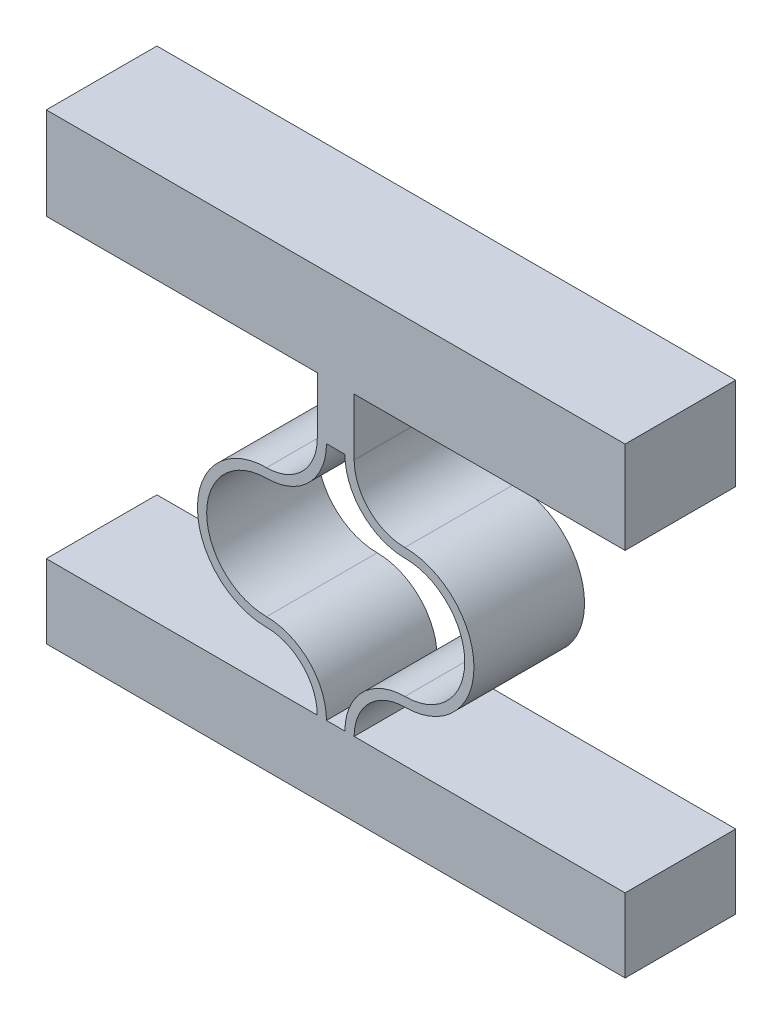
SolidWorks part; units mm, degrees
ref_plane "Front Plane" through (0, 0, 0) normal (0, 0, 1) x (1, 0, 0)
ref_plane "Top Plane" through (0, 0, 0) normal (0, 1, 0) x (1, 0, 0)
ref_plane "Right Plane" through (0, 0, 0) normal (1, 0, 0) x (0, 0, -1)
sketch "Sketch1" plane through (0, 0, 0) normal (0, 0, 1) x (1, 0, 0)
  line L4 (0, 10.5) -> (0, 0)
  line L5 (10.2, 0) -> (10.2, 13) construction
  line L6 (10.2, 13) -> (10.2, 15.9852) construction
  line L17 (9.7, 0) -> (0, 0)
  line L18 (10.7, 0) -> (20.4, 0)
  line L19 (20.4, 0) -> (20.4, 10.5)
  line L20 (10.7, 13.2452) -> (10.7, 14.4852)
  line L21 (9.7, 13.2452) -> (9.7, 14.4852)
  line L22 (10.7, 14.7452) -> (10.7, 15.9852)
  line L23 (10.7, 15.9852) -> (9.7, 15.9852)
  line L24 (9.7, 15.9852) -> (9.7, 14.7452)
  line L31 (-5, 12.26) -> (-5, -4)
  line L32 (-5, -4) -> (25.4, -4)
  line L33 (25.4, -4) -> (25.4, 12.26)
  line L34 (0, 10.76) -> (0, 12)
  line L36 (-5, 12.26) -> (0, 12.26)
  line L37 (25.4, 12.26) -> (20.4, 12.26)
  line L38 (20.4, 10.76) -> (20.4, 12)
  arc A0 (10.2, 13) -> (6.95, 9.75) centre (6.95, 13) cw
  arc A1 (6.95, 9.75) -> (6.95, 3.25) centre (6.95, 6.5) ccw
  arc A2 (6.95, 3.25) -> (10.2, 0) centre (6.95, 0) cw
  arc A3 (9.7, 12.9852) -> (6.95, 10.25) centre (6.95, 13) cw
  arc A4 (6.95, 10.25) -> (6.95, 2.75) centre (6.95, 6.5) ccw
  arc A5 (6.95, 2.75) -> (9.7, 0) centre (6.95, 0) cw
  arc A6 (9.7, 13) -> (6.95, 10.25) centre (6.95, 13) cw construction
  arc A7 (13.45, 3.25) -> (10.2, 0) centre (13.45, 0) ccw
  arc A8 (13.45, 2.75) -> (10.7, 0) centre (13.45, 0) ccw
  arc A9 (13.45, 9.75) -> (13.45, 3.25) centre (13.45, 6.5) cw
  arc A10 (13.45, 10.25) -> (13.45, 2.75) centre (13.45, 6.5) cw
  arc A11 (10.7, 12.9852) -> (13.45, 10.25) centre (13.45, 13) ccw
  arc A12 (10.2, 13) -> (13.45, 9.75) centre (13.45, 13) ccw
  spline S0 degree 4 poles (-2.0399, 10.9987) (-1.9769, 10.9844) (-1.8506, 10.9568) (-1.6594, 10.9185) (-1.4063, 10.8738) (-1.1473, 10.836) (-0.8994, 10.8056) (-0.6275, 10.7825) (-0.4084, 10.7671) (-0.0945, 10.7598) (0.0489, 10.7593) (0.3554, 10.7653) (0.5833, 10.7785) (0.8327, 10.7992) (1.1232, 10.8326) (1.4148, 10.8743) (1.7521, 10.9345) (2.2064, 11.0333) (2.726, 11.1697) (3.2397, 11.3281) (3.7479, 11.5024) (4.1845, 11.6613) (4.5513, 11.7992) (4.9172, 11.9395) (5.2828, 12.0805) (5.7402, 12.2559) (6.427, 12.5125) (7.2136, 12.7819) (8.1107, 13.0284) (9.0261, 13.1932) (9.8075, 13.2661) (10.5925, 13.2661) (11.3739, 13.1932) (12.2893, 13.0284) (13.1864, 12.7819) (13.973, 12.5125) (14.6598, 12.2559) (15.2087, 12.0455) (15.6656, 11.8688) (16.1235, 11.6948) (16.6521, 11.5024) (17.1603, 11.3281) (17.6739, 11.1697) (18.1937, 11.0333) (18.5999, 10.9449) (18.8889, 10.8915) (19.1309, 10.8534) (19.3251, 10.827) (19.5196, 10.8048) (19.7158, 10.7868) (19.909, 10.7733) (20.1017, 10.7642) (20.3513, 10.7593) (20.4943, 10.7598) (20.8085, 10.7671) (21.0274, 10.7825) (21.2994, 10.8056) (21.5473, 10.836) (21.8063, 10.8738) (22.0594, 10.9185) (22.2506, 10.9568) (22.3769, 10.9844) (22.4399, 10.9987) knots 0 0 0 0 0 0.010251 0.020502 0.030753 0.041005 0.05113 0.061255 0.071381 0.081506 0.089265 0.097024 0.112543 0.120302 0.128061 0.143579 0.159098 0.174616 0.201648 0.22868 0.244198 0.259716 0.275235 0.290753 0.306271 0.32179 0.352826 0.40689 0.437927 0.468963 0.5 0.531037 0.562073 0.59311 0.647174 0.67821 0.693729 0.709247 0.740284 0.755802 0.77132 0.798352 0.825384 0.840902 0.856421 0.86418 0.871939 0.879698 0.887457 0.895217 0.902976 0.910735 0.918494 0.928619 0.938745 0.94887 0.958995 0.969247 0.979498 0.989749 1 1 1 1 1 construction
  spline S1 degree 4 poles (0, 10.76) (0.041, 10.76) (0.1243, 10.7608) (0.3554, 10.7653) (0.5833, 10.7785) (0.8327, 10.7992) (1.1232, 10.8326) (1.4148, 10.8743) (1.7521, 10.9345) (2.2064, 11.0333) (2.726, 11.1697) (3.2397, 11.3281) (3.7479, 11.5024) (4.1845, 11.6613) (4.5513, 11.7992) (4.9172, 11.9395) (5.2828, 12.0805) (5.7402, 12.2559) (6.427, 12.5125) (7.2136, 12.7819) (8.1107, 13.0284) (9.0261, 13.1932) (9.8075, 13.2661) (10.5925, 13.2661) (11.3739, 13.1932) (12.2893, 13.0284) (13.1864, 12.7819) (13.973, 12.5125) (14.6598, 12.2559) (15.2087, 12.0455) (15.6656, 11.8688) (16.1235, 11.6948) (16.6521, 11.5024) (17.1603, 11.3281) (17.6739, 11.1697) (18.1937, 11.0333) (18.5999, 10.9449) (18.8889, 10.8915) (19.1309, 10.8534) (19.3251, 10.827) (19.5196, 10.8048) (19.7158, 10.7868) (19.909, 10.7733) (20.1017, 10.7642) (20.2757, 10.7608) (20.359, 10.76) (20.4, 10.76) knots 0.081506 0.081506 0.081506 0.081506 0.081506 0.089265 0.097024 0.112543 0.120302 0.128061 0.143579 0.159098 0.174616 0.201648 0.22868 0.244198 0.259716 0.275235 0.290753 0.306271 0.32179 0.352826 0.40689 0.437927 0.468963 0.5 0.531037 0.562073 0.59311 0.647174 0.67821 0.693729 0.709247 0.740284 0.755802 0.77132 0.798352 0.825384 0.840902 0.856421 0.86418 0.871939 0.879698 0.887457 0.895217 0.902976 0.910735 0.918494 0.918494 0.918494 0.918494 0.918494
  spline S2 degree 4 poles (-2.0399, 12.2387) (-1.9769, 12.2244) (-1.8506, 12.1968) (-1.6594, 12.1585) (-1.4063, 12.1138) (-1.1473, 12.076) (-0.8994, 12.0456) (-0.6275, 12.0225) (-0.4084, 12.0071) (-0.0945, 11.9998) (0.0489, 11.9993) (0.3554, 12.0053) (0.5833, 12.0185) (0.8327, 12.0392) (1.1232, 12.0726) (1.4148, 12.1143) (1.7521, 12.1745) (2.2064, 12.2733) (2.726, 12.4097) (3.2397, 12.5681) (3.7479, 12.7424) (4.1845, 12.9013) (4.5513, 13.0392) (4.9172, 13.1795) (5.2828, 13.3205) (5.7402, 13.4959) (6.427, 13.7525) (7.2136, 14.0219) (8.1107, 14.2684) (9.0261, 14.4332) (9.8075, 14.5061) (10.5925, 14.5061) (11.3739, 14.4332) (12.2893, 14.2684) (13.1864, 14.0219) (13.973, 13.7525) (14.6598, 13.4959) (15.2087, 13.2855) (15.6656, 13.1088) (16.1235, 12.9348) (16.6521, 12.7424) (17.1603, 12.5681) (17.6739, 12.4097) (18.1937, 12.2733) (18.5999, 12.1849) (18.8889, 12.1315) (19.1309, 12.0934) (19.3251, 12.067) (19.5196, 12.0448) (19.7158, 12.0268) (19.909, 12.0133) (20.1017, 12.0042) (20.3513, 11.9993) (20.4943, 11.9998) (20.8085, 12.0071) (21.0274, 12.0225) (21.2994, 12.0456) (21.5473, 12.076) (21.8063, 12.1138) (22.0594, 12.1585) (22.2506, 12.1968) (22.3769, 12.2244) (22.4399, 12.2387) knots 0 0 0 0 0 0.010251 0.020502 0.030753 0.041005 0.05113 0.061255 0.071381 0.081506 0.089265 0.097024 0.112543 0.120302 0.128061 0.143579 0.159098 0.174616 0.201648 0.22868 0.244198 0.259716 0.275235 0.290753 0.306271 0.32179 0.352826 0.40689 0.437927 0.468963 0.5 0.531037 0.562073 0.59311 0.647174 0.67821 0.693729 0.709247 0.740284 0.755802 0.77132 0.798352 0.825384 0.840902 0.856421 0.86418 0.871939 0.879698 0.887457 0.895217 0.902976 0.910735 0.918494 0.928619 0.938745 0.94887 0.958995 0.969247 0.979498 0.989749 1 1 1 1 1 construction
  spline S3 degree 4 poles (0, 12) (0.041, 12) (0.1243, 12.0008) (0.3554, 12.0053) (0.5833, 12.0185) (0.8327, 12.0392) (1.1232, 12.0726) (1.4148, 12.1143) (1.7521, 12.1745) (2.2064, 12.2733) (2.726, 12.4097) (3.2397, 12.5681) (3.7479, 12.7424) (4.1845, 12.9013) (4.5513, 13.0392) (4.9172, 13.1795) (5.2828, 13.3205) (5.7402, 13.4959) (6.427, 13.7525) (7.2136, 14.0219) (8.1107, 14.2684) (9.0261, 14.4332) (9.8075, 14.5061) (10.5925, 14.5061) (11.3739, 14.4332) (12.2893, 14.2684) (13.1864, 14.0219) (13.973, 13.7525) (14.6598, 13.4959) (15.2087, 13.2855) (15.6656, 13.1088) (16.1235, 12.9348) (16.6521, 12.7424) (17.1603, 12.5681) (17.6739, 12.4097) (18.1937, 12.2733) (18.5999, 12.1849) (18.8889, 12.1315) (19.1309, 12.0934) (19.3251, 12.067) (19.5196, 12.0448) (19.7158, 12.0268) (19.909, 12.0133) (20.1017, 12.0042) (20.2757, 12.0008) (20.359, 12) (20.4, 12) knots 0.081506 0.081506 0.081506 0.081506 0.081506 0.089265 0.097024 0.112543 0.120302 0.128061 0.143579 0.159098 0.174616 0.201648 0.22868 0.244198 0.259716 0.275235 0.290753 0.306271 0.32179 0.352826 0.40689 0.437927 0.468963 0.5 0.531037 0.562073 0.59311 0.647174 0.67821 0.693729 0.709247 0.740284 0.755802 0.77132 0.798352 0.825384 0.840902 0.856421 0.86418 0.871939 0.879698 0.887457 0.895217 0.902976 0.910735 0.918494 0.918494 0.918494 0.918494 0.918494
  spline S4 degree 4 poles (-2.0399, 12.4987) (-1.9769, 12.4844) (-1.8506, 12.4568) (-1.6594, 12.4185) (-1.4063, 12.3738) (-1.1473, 12.336) (-0.8994, 12.3056) (-0.6275, 12.2825) (-0.4084, 12.2671) (-0.0945, 12.2598) (0.0489, 12.2593) (0.3554, 12.2653) (0.5833, 12.2785) (0.8327, 12.2992) (1.1232, 12.3326) (1.4148, 12.3743) (1.7521, 12.4345) (2.2064, 12.5333) (2.726, 12.6697) (3.2397, 12.8281) (3.7479, 13.0024) (4.1845, 13.1613) (4.5513, 13.2992) (4.9172, 13.4395) (5.2828, 13.5805) (5.7402, 13.7559) (6.427, 14.0125) (7.2136, 14.2819) (8.1107, 14.5284) (9.0261, 14.6932) (9.8075, 14.7661) (10.5925, 14.7661) (11.3739, 14.6932) (12.2893, 14.5284) (13.1864, 14.2819) (13.973, 14.0125) (14.6598, 13.7559) (15.2087, 13.5455) (15.6656, 13.3688) (16.1235, 13.1948) (16.6521, 13.0024) (17.1603, 12.8281) (17.6739, 12.6697) (18.1937, 12.5333) (18.5999, 12.4449) (18.8889, 12.3915) (19.1309, 12.3534) (19.3251, 12.327) (19.5196, 12.3048) (19.7158, 12.2868) (19.909, 12.2733) (20.1017, 12.2642) (20.3513, 12.2593) (20.4943, 12.2598) (20.8085, 12.2671) (21.0274, 12.2825) (21.2994, 12.3056) (21.5473, 12.336) (21.8063, 12.3738) (22.0594, 12.4185) (22.2506, 12.4568) (22.3769, 12.4844) (22.4399, 12.4987) knots 0 0 0 0 0 0.010251 0.020502 0.030753 0.041005 0.05113 0.061255 0.071381 0.081506 0.089265 0.097024 0.112543 0.120302 0.128061 0.143579 0.159098 0.174616 0.201648 0.22868 0.244198 0.259716 0.275235 0.290753 0.306271 0.32179 0.352826 0.40689 0.437927 0.468963 0.5 0.531037 0.562073 0.59311 0.647174 0.67821 0.693729 0.709247 0.740284 0.755802 0.77132 0.798352 0.825384 0.840902 0.856421 0.86418 0.871939 0.879698 0.887457 0.895217 0.902976 0.910735 0.918494 0.928619 0.938745 0.94887 0.958995 0.969247 0.979498 0.989749 1 1 1 1 1 construction
  spline S5 degree 4 poles (0, 12.26) (0.041, 12.26) (0.1243, 12.2608) (0.3554, 12.2653) (0.5833, 12.2785) (0.8327, 12.2992) (1.1232, 12.3326) (1.4148, 12.3743) (1.7521, 12.4345) (2.2064, 12.5333) (2.726, 12.6697) (3.2397, 12.8281) (3.7479, 13.0024) (4.1845, 13.1613) (4.5513, 13.2992) (4.9172, 13.4395) (5.2828, 13.5805) (5.7402, 13.7559) (6.427, 14.0125) (7.2136, 14.2819) (8.1107, 14.5284) (9.0261, 14.6932) (9.8075, 14.7661) (10.5925, 14.7661) (11.3739, 14.6932) (12.2893, 14.5284) (13.1864, 14.2819) (13.973, 14.0125) (14.6598, 13.7559) (15.2087, 13.5455) (15.6656, 13.3688) (16.1235, 13.1948) (16.6521, 13.0024) (17.1603, 12.8281) (17.6739, 12.6697) (18.1937, 12.5333) (18.5999, 12.4449) (18.8889, 12.3915) (19.1309, 12.3534) (19.3251, 12.327) (19.5196, 12.3048) (19.7158, 12.2868) (19.909, 12.2733) (20.1017, 12.2642) (20.2757, 12.2608) (20.359, 12.26) (20.4, 12.26) knots 0.081506 0.081506 0.081506 0.081506 0.081506 0.089265 0.097024 0.112543 0.120302 0.128061 0.143579 0.159098 0.174616 0.201648 0.22868 0.244198 0.259716 0.275235 0.290753 0.306271 0.32179 0.352826 0.40689 0.437927 0.468963 0.5 0.531037 0.562073 0.59311 0.647174 0.67821 0.693729 0.709247 0.740284 0.755802 0.77132 0.798352 0.825384 0.840902 0.856421 0.86418 0.871939 0.879698 0.887457 0.895217 0.902976 0.910735 0.918494 0.918494 0.918494 0.918494 0.918494
  spline S8 degree 4 poles (-2.0399, 10.7387) (-1.9769, 10.7244) (-1.8506, 10.6968) (-1.6594, 10.6585) (-1.4063, 10.6138) (-1.1473, 10.576) (-0.8994, 10.5456) (-0.6275, 10.5225) (-0.4084, 10.5071) (-0.0945, 10.4998) (0.0489, 10.4993) (0.3554, 10.5053) (0.5833, 10.5185) (0.8327, 10.5392) (1.1232, 10.5726) (1.4148, 10.6143) (1.7521, 10.6745) (2.2064, 10.7733) (2.726, 10.9097) (3.2397, 11.0681) (3.7479, 11.2424) (4.1845, 11.4013) (4.5513, 11.5392) (4.9172, 11.6795) (5.2828, 11.8205) (5.7402, 11.9959) (6.427, 12.2525) (7.2136, 12.5219) (8.1107, 12.7684) (9.0261, 12.9332) (9.8075, 13.0061) (10.5925, 13.0061) (11.3739, 12.9332) (12.2893, 12.7684) (13.1864, 12.5219) (13.973, 12.2525) (14.6598, 11.9959) (15.2087, 11.7855) (15.6656, 11.6088) (16.1235, 11.4348) (16.6521, 11.2424) (17.1603, 11.0681) (17.6739, 10.9097) (18.1937, 10.7733) (18.5999, 10.6849) (18.8889, 10.6315) (19.1309, 10.5934) (19.3251, 10.567) (19.5196, 10.5448) (19.7158, 10.5268) (19.909, 10.5133) (20.1017, 10.5042) (20.3513, 10.4993) (20.4943, 10.4998) (20.8085, 10.5071) (21.0274, 10.5225) (21.2994, 10.5456) (21.5473, 10.576) (21.8063, 10.6138) (22.0594, 10.6585) (22.2506, 10.6968) (22.3769, 10.7244) (22.4399, 10.7387) knots 0 0 0 0 0 0.010251 0.020502 0.030753 0.041005 0.05113 0.061255 0.071381 0.081506 0.089265 0.097024 0.112543 0.120302 0.128061 0.143579 0.159098 0.174616 0.201648 0.22868 0.244198 0.259716 0.275235 0.290753 0.306271 0.32179 0.352826 0.40689 0.437927 0.468963 0.5 0.531037 0.562073 0.59311 0.647174 0.67821 0.693729 0.709247 0.740284 0.755802 0.77132 0.798352 0.825384 0.840902 0.856421 0.86418 0.871939 0.879698 0.887457 0.895217 0.902976 0.910735 0.918494 0.928619 0.938745 0.94887 0.958995 0.969247 0.979498 0.989749 1 1 1 1 1 construction
  spline S9 degree 4 poles (0, 10.5) (0.041, 10.5) (0.1243, 10.5008) (0.3554, 10.5053) (0.5833, 10.5185) (0.8327, 10.5392) (1.1232, 10.5726) (1.4148, 10.6143) (1.7521, 10.6745) (2.2064, 10.7733) (2.726, 10.9097) (3.2397, 11.0681) (3.7479, 11.2424) (4.1845, 11.4013) (4.5513, 11.5392) (4.9172, 11.6795) (5.2828, 11.8205) (5.7402, 11.9959) (6.427, 12.2525) (7.2136, 12.5219) (8.1107, 12.7684) (9.0261, 12.9332) (9.8075, 13.0061) (10.5925, 13.0061) (11.3739, 12.9332) (12.2893, 12.7684) (13.1864, 12.5219) (13.973, 12.2525) (14.6598, 11.9959) (15.2087, 11.7855) (15.6656, 11.6088) (16.1235, 11.4348) (16.6521, 11.2424) (17.1603, 11.0681) (17.6739, 10.9097) (18.1937, 10.7733) (18.5999, 10.6849) (18.8889, 10.6315) (19.1309, 10.5934) (19.3251, 10.567) (19.5196, 10.5448) (19.7158, 10.5268) (19.909, 10.5133) (20.1017, 10.5042) (20.2757, 10.5008) (20.359, 10.5) (20.4, 10.5) knots 0.081506 0.081506 0.081506 0.081506 0.081506 0.089265 0.097024 0.112543 0.120302 0.128061 0.143579 0.159098 0.174616 0.201648 0.22868 0.244198 0.259716 0.275235 0.290753 0.306271 0.32179 0.352826 0.40689 0.437927 0.468963 0.5 0.531037 0.562073 0.59311 0.647174 0.67821 0.693729 0.709247 0.740284 0.755802 0.77132 0.798352 0.825384 0.840902 0.856421 0.86418 0.871939 0.879698 0.887457 0.895217 0.902976 0.910735 0.918494 0.918494 0.918494 0.918494 0.918494
  dimension "D4" = 0.26
  dimension "D6" = 4
  dimension "D1" = 13
  dimension "D2" = 0.5
  dimension "D3" = 0.26
  dimension "D7" = 5
  dimension "D5" = 1.5
extrude "Boss-Extrude1" add sketch "Sketch1" along normal blind 6
sketch "Sketch4" plane through (0, 15.9852, 0) normal (0, 1, 0) x (1, 0, 0)
  line L24 (10.7, 0) -> (9.7, 0)
  line L25 (9.7, 0) -> (9.7, -6)
  line L26 (10.7, 0) -> (9.7, 0)
  line L27 (10.7, -6) -> (10.7, 0)
  line L29 (9.7, 0) -> (9.7, -6)
  line L31 (10.7, -6) -> (10.7, 0)
  line L32 (9.7, -6) -> (10.7, -6)
  line L33 (9.7, -6) -> (10.7, -6)
  dimension "D1" = 0
extrude "Boss-Extrude2" add sketch "Sketch4" along normal blind 0.1
mirror "Mirror3" [suppressed]
ref_plane "Plane1" through (10.2, 0, 0) normal (-1, 0, 0) x (0, 0, 1)
split "Split2" trim tools "Plane1" bodies to split 179 102 resulting bodies 225
sketch "Sketch7" plane through (10.2, 0, 0) normal (-1, 0, 0) x (0, 0, 1)
  line L4 (0, 13) -> (6, 13)
  line L12 (0, 13) -> (6, 13)
  line L13 (0, 13) -> (6, 13)
  line L14 (6, 13) -> (6, 16.0852)
  line L15 (6, 13) -> (6, 16.0852)
  line L20 (6, 0) -> (0, 0)
  line L22 (6, 0) -> (0, 0)
  line L23 (0, -4) -> (6, -4)
  line L27 (0, -4) -> (6, -4)
  line L31 (6, 16.0852) -> (0, 16.0852)
  line L33 (0, 16.0852) -> (0, 13)
  line L34 (0, 16.0852) -> (0, 13)
  line L36 (6, -4) -> (6, 0)
  line L38 (0, 13) -> (6, 13)
  line L39 (0, 13) -> (6, 13)
  line L40 (6, 13) -> (6, 16.0852)
  line L41 (6, 13) -> (6, 16.0852)
  line L51 (6, 16.0852) -> (0, 16.0852)
  line L52 (6, 16.0852) -> (0, 16.0852)
  line L53 (0, 16.0852) -> (0, 13)
  line L54 (0, 16.0852) -> (0, 13)
  line L55 (0, 13) -> (6, 13)
  line L59 (6, -4) -> (6, 0)
  line L60 (0, 0) -> (0, -4)
  line L61 (0, 0) -> (0, -4)
  line L62 (6, 13) -> (6, 16.0852)
  line L64 (6, 13) -> (6, 16.0852)
  line L66 (6, 16.0852) -> (0, 16.0852)
  line L67 (6, 16.0852) -> (0, 16.0852)
  line L68 (0, 16.0852) -> (0, 13)
  line L69 (0, 16.0852) -> (0, 13)
  line L70 (6, 16.0852) -> (0, 16.0852)
  dimension "D1" = 0
  dimension "D2" = 0
  dimension "D3" = 0
  dimension "D4" = 0
extrude "Boss-Extrude3" add sketch "Sketch7" along normal blind 0.5
mirror "Mirror2" about plane through (9.7, 0, 0) normal (-1, 0, 0) of bodies 226
sketch "Sketch8" plane through (0, 0, 6) normal (0, 0, 1) x (1, 0, 0)
  line L0 (25.4, 12.26) -> (20.4, 12.26) construction
  line L1 (-6, 21.0852) -> (25.4, 21.0852)
  line L2 (-6, 21.0852) -> (-6, 16.0852)
  line L3 (-6, 16.0852) -> (25.4, 16.0852)
  line L4 (25.4, 21.0852) -> (25.4, 16.0852)
  line L5 (25.4, -4) -> (25.4, 12.26) construction
  line L6 (-6, -4) -> (-6, 12.26) construction
  line L7 (8.7, 16.0852) -> (10.7, 16.0852) construction
extrude "Boss-Extrude4" add sketch "Sketch8" against normal up to surface (6 mm away) up to face at (9.7, 10.5186, 0)
sketch "Sketch9" plane through (0, 0, 6) normal (0, 0, 1) x (1, 0, 0)
  line L0 (-1, 10.5) -> (-1, 12.26)
  line L1 (20.4, 10.5) -> (20.4, 12.26)
  line L2 (10.7, 14.7452) -> (10.7, 12.9852)
  line L3 (8.7, 12.9852) -> (8.7, 14.7452)
  spline S0 degree 4 poles (-508.9824, 1946.5317) (8.084, -72.7533) (31.0872, 1.6312) (18.0938, 16.5066) (7.1107, 14.5284) (6.2136, 14.2819) (5.427, 14.0125) (4.7402, 13.7559) (4.1913, 13.5455) (3.7344, 13.3688) (3.2765, 13.1948) (2.7479, 13.0024) (2.2397, 12.8281) (1.7261, 12.6697) (1.2063, 12.5333) (0.8001, 12.4449) (0.5111, 12.3915) (0.2691, 12.3534) (0.0749, 12.327) (-0.1196, 12.3048) (-0.3158, 12.2868) (-0.509, 12.2733) (-1.6254, 12.2207) (-4.3016, 12.3558) (45.9369, 12.6644) (-2000.0599, 12.9471) knots -1.118658 -1.118658 -1.118658 -1.118658 -1.118658 0.531037 0.562073 0.59311 0.647174 0.67821 0.693729 0.709247 0.740284 0.755802 0.77132 0.798352 0.825384 0.840902 0.856421 0.86418 0.871939 0.879698 0.887457 0.895217 0.902976 0.910735 1.067273 1.067273 1.067273 1.067273 1.067273 only from (8.7, 14.7452) to (-1, 12.26) construction
  spline S1 degree 4 poles (-508.9824, 1944.7717) (8.084, -74.5133) (31.0872, -0.1288) (18.0938, 14.7466) (7.1107, 12.7684) (6.2136, 12.5219) (5.427, 12.2525) (4.7402, 11.9959) (4.1913, 11.7855) (3.7344, 11.6088) (3.2765, 11.4348) (2.7479, 11.2424) (2.2397, 11.0681) (1.7261, 10.9097) (1.2063, 10.7733) (0.8001, 10.6849) (0.5111, 10.6315) (0.2691, 10.5934) (0.0749, 10.567) (-0.1196, 10.5448) (-0.3158, 10.5268) (-0.509, 10.5133) (-1.6254, 10.4607) (-4.3016, 10.5958) (45.9369, 10.9044) (-2000.0599, 11.1871) knots -1.118658 -1.118658 -1.118658 -1.118658 -1.118658 0.531037 0.562073 0.59311 0.647174 0.67821 0.693729 0.709247 0.740284 0.755802 0.77132 0.798352 0.825384 0.840902 0.856421 0.86418 0.871939 0.879698 0.887457 0.895217 0.902976 0.910735 1.067273 1.067273 1.067273 1.067273 1.067273 only from (8.7, 12.9852) to (-1, 10.5) construction
  spline S2 degree 4 poles (528.3824, 1944.7717) (11.316, -74.5133) (-11.6872, -0.1288) (1.3062, 14.7466) (12.2893, 12.7684) (13.1864, 12.5219) (13.973, 12.2525) (14.6598, 11.9959) (15.2087, 11.7855) (15.6656, 11.6088) (16.1235, 11.4348) (16.6521, 11.2424) (17.1603, 11.0681) (17.6739, 10.9097) (18.1937, 10.7733) (18.5999, 10.6849) (18.8889, 10.6315) (19.1309, 10.5934) (19.3251, 10.567) (19.5196, 10.5448) (19.7158, 10.5268) (19.909, 10.5133) (21.0254, 10.4607) (23.7016, 10.5958) (-26.5369, 10.9044) (2019.4599, 11.1871) knots -1.118658 -1.118658 -1.118658 -1.118658 -1.118658 0.531037 0.562073 0.59311 0.647174 0.67821 0.693729 0.709247 0.740284 0.755802 0.77132 0.798352 0.825384 0.840902 0.856421 0.86418 0.871939 0.879698 0.887457 0.895217 0.902976 0.910735 1.067273 1.067273 1.067273 1.067273 1.067273 only from (10.7, 12.9852) to (20.4, 10.5) construction
  spline S3 degree 4 poles (528.3824, 1946.5317) (11.316, -72.7533) (-11.6872, 1.6312) (1.3062, 16.5066) (12.2893, 14.5284) (13.1864, 14.2819) (13.973, 14.0125) (14.6598, 13.7559) (15.2087, 13.5455) (15.6656, 13.3688) (16.1235, 13.1948) (16.6521, 13.0024) (17.1603, 12.8281) (17.6739, 12.6697) (18.1937, 12.5333) (18.5999, 12.4449) (18.8889, 12.3915) (19.1309, 12.3534) (19.3251, 12.327) (19.5196, 12.3048) (19.7158, 12.2868) (19.909, 12.2733) (21.0254, 12.2207) (23.7016, 12.3558) (-26.5369, 12.6644) (2019.4599, 12.9471) knots -1.118658 -1.118658 -1.118658 -1.118658 -1.118658 0.531037 0.562073 0.59311 0.647174 0.67821 0.693729 0.709247 0.740284 0.755802 0.77132 0.798352 0.825384 0.840902 0.856421 0.86418 0.871939 0.879698 0.887457 0.895217 0.902976 0.910735 1.067273 1.067273 1.067273 1.067273 1.067273 only from (10.7, 14.7452) to (20.4, 12.26) construction
  spline S4 degree 4 poles (8.7, 14.7452) (8.6292, 14.741) (8.3631, 14.7224) (7.9029, 14.671) (7.1107, 14.5284) (6.2136, 14.2819) (5.427, 14.0125) (4.7402, 13.7559) (4.1913, 13.5455) (3.7344, 13.3688) (3.2765, 13.1948) (2.7479, 13.0024) (2.2397, 12.8281) (1.7261, 12.6697) (1.2063, 12.5333) (0.8001, 12.4449) (0.5111, 12.3915) (0.2691, 12.3534) (0.0749, 12.327) (-0.1196, 12.3048) (-0.3158, 12.2868) (-0.509, 12.2733) (-0.7017, 12.2642) (-0.8757, 12.2608) (-0.959, 12.26) (-1, 12.26) knots 0.519813 0.519813 0.519813 0.519813 0.519813 0.531037 0.562073 0.59311 0.647174 0.67821 0.693729 0.709247 0.740284 0.755802 0.77132 0.798352 0.825384 0.840902 0.856421 0.86418 0.871939 0.879698 0.887457 0.895217 0.902976 0.910735 0.918494 0.918494 0.918494 0.918494 0.918494
  spline S5 degree 4 poles (8.7, 12.9852) (8.6292, 12.981) (8.3631, 12.9624) (7.9029, 12.911) (7.1107, 12.7684) (6.2136, 12.5219) (5.427, 12.2525) (4.7402, 11.9959) (4.1913, 11.7855) (3.7344, 11.6088) (3.2765, 11.4348) (2.7479, 11.2424) (2.2397, 11.0681) (1.7261, 10.9097) (1.2063, 10.7733) (0.8001, 10.6849) (0.5111, 10.6315) (0.2691, 10.5934) (0.0749, 10.567) (-0.1196, 10.5448) (-0.3158, 10.5268) (-0.509, 10.5133) (-0.7017, 10.5042) (-0.8757, 10.5008) (-0.959, 10.5) (-1, 10.5) knots 0.519813 0.519813 0.519813 0.519813 0.519813 0.531037 0.562073 0.59311 0.647174 0.67821 0.693729 0.709247 0.740284 0.755802 0.77132 0.798352 0.825384 0.840902 0.856421 0.86418 0.871939 0.879698 0.887457 0.895217 0.902976 0.910735 0.918494 0.918494 0.918494 0.918494 0.918494
  spline S6 degree 4 poles (10.7, 12.9852) (10.7708, 12.981) (11.0369, 12.9624) (11.4971, 12.911) (12.2893, 12.7684) (13.1864, 12.5219) (13.973, 12.2525) (14.6598, 11.9959) (15.2087, 11.7855) (15.6656, 11.6088) (16.1235, 11.4348) (16.6521, 11.2424) (17.1603, 11.0681) (17.6739, 10.9097) (18.1937, 10.7733) (18.5999, 10.6849) (18.8889, 10.6315) (19.1309, 10.5934) (19.3251, 10.567) (19.5196, 10.5448) (19.7158, 10.5268) (19.909, 10.5133) (20.1017, 10.5042) (20.2757, 10.5008) (20.359, 10.5) (20.4, 10.5) knots 0.519813 0.519813 0.519813 0.519813 0.519813 0.531037 0.562073 0.59311 0.647174 0.67821 0.693729 0.709247 0.740284 0.755802 0.77132 0.798352 0.825384 0.840902 0.856421 0.86418 0.871939 0.879698 0.887457 0.895217 0.902976 0.910735 0.918494 0.918494 0.918494 0.918494 0.918494
  spline S7 degree 4 poles (10.7, 14.7452) (10.7708, 14.741) (11.0369, 14.7224) (11.4971, 14.671) (12.2893, 14.5284) (13.1864, 14.2819) (13.973, 14.0125) (14.6598, 13.7559) (15.2087, 13.5455) (15.6656, 13.3688) (16.1235, 13.1948) (16.6521, 13.0024) (17.1603, 12.8281) (17.6739, 12.6697) (18.1937, 12.5333) (18.5999, 12.4449) (18.8889, 12.3915) (19.1309, 12.3534) (19.3251, 12.327) (19.5196, 12.3048) (19.7158, 12.2868) (19.909, 12.2733) (20.1017, 12.2642) (20.2757, 12.2608) (20.359, 12.26) (20.4, 12.26) knots 0.519813 0.519813 0.519813 0.519813 0.519813 0.531037 0.562073 0.59311 0.647174 0.67821 0.693729 0.709247 0.740284 0.755802 0.77132 0.798352 0.825384 0.840902 0.856421 0.86418 0.871939 0.879698 0.887457 0.895217 0.902976 0.910735 0.918494 0.918494 0.918494 0.918494 0.918494
extrude "Cut-Extrude1" cut sketch "Sketch9" against normal through all
sketch "Sketch10" plane through (0, 0, 6) normal (0, 0, 1) x (1, 0, 0)
  line L0 (25.4, -4) -> (25.4, 12.26) construction
  line L1 (-6, 12.26) -> (-1, 12.26)
  line L2 (-6, 12.26) -> (-6, 0)
  line L3 (-6, 0) -> (-1, 0)
  line L4 (-1, 12.26) -> (-1, 0)
  line L5 (20.4, 12.26) -> (25.4, 12.26)
  line L6 (20.4, 12.26) -> (20.4, 0)
  line L7 (20.4, 0) -> (25.4, 0)
  line L8 (25.4, 12.26) -> (25.4, 0)
extrude "Cut-Extrude2" cut sketch "Sketch10" against normal through all
